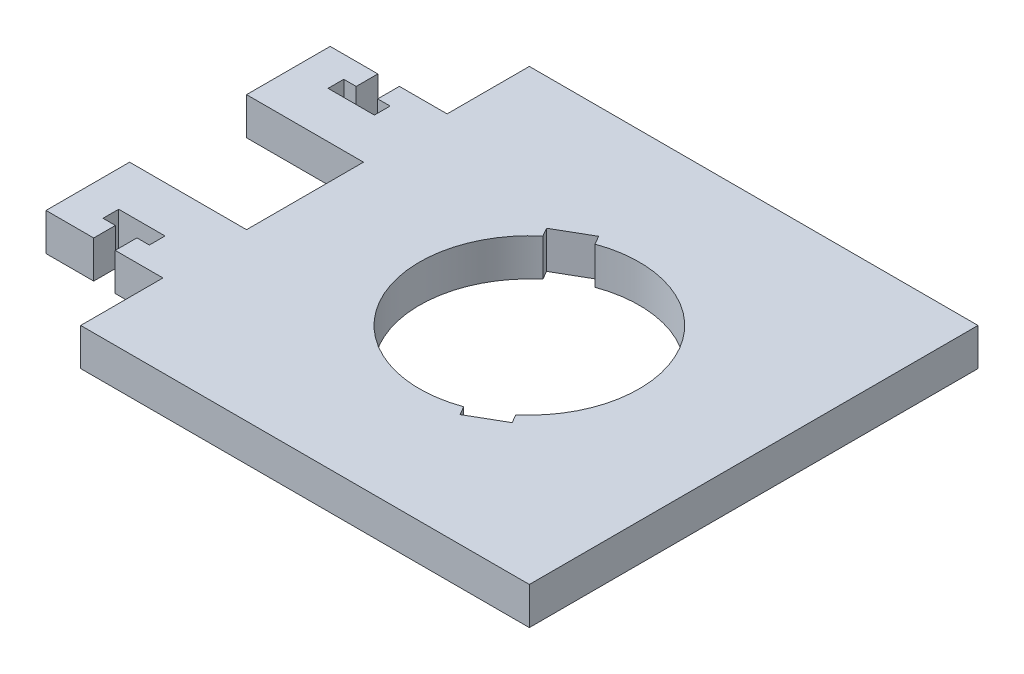
SolidWorks part; units mm, degrees
ref_plane "Front Plane" through (0, 0, 0) normal (0, 0, 1) x (1, 0, 0)
ref_plane "Top Plane" through (0, 0, 0) normal (0, 1, 0) x (1, 0, 0)
ref_plane "Right Plane" through (0, 0, 0) normal (1, 0, 0) x (0, 0, -1)
sketch "Sketch1" plane through (0, 0, 0) normal (0, 1, 0) x (1, 0, 0)
  line L0 (0, 0) -> (38.1, 0) construction
  line L1 (-38.1, -38.1) -> (38.1, -38.1)
  line L2 (-38.1, -38.1) -> (-38.1, -24.13)
  line L3 (-38.1, 38.1) -> (38.1, 38.1)
  line L4 (38.1, -38.1) -> (38.1, 38.1)
  line L5 (-38.1, -38.1) -> (38.1, 38.1) construction
  line L6 (-38.1, 38.1) -> (38.1, -38.1) construction
  line L7 (0, 0) -> (0, -18.5806) construction
  line L8 (9.2265, -15.9809) -> (10.033, -17.3776) construction
  line L11 (7.2271, -18.9976) -> (12.8389, -15.7576)
  line L12 (7.2271, -18.9976) -> (6.3819, -17.5338)
  line L14 (12.8389, -15.7576) -> (11.9937, -14.2938)
  line L15 (0, 0) -> (8.5457, 4.9338) construction
  line L17 (-7.2271, 18.9976) -> (-6.3819, 17.5338)
  line L18 (-12.8389, 15.7576) -> (-7.2271, 18.9976)
  line L19 (-12.8389, 15.7576) -> (-11.9937, 14.2938)
  line L20 (-38.1, -38.1) -> (-38.1, -24.13) construction
  line L21 (-38.1, -24.13) -> (-46.2026, -24.13)
  line L22 (-57.9628, -24.13) -> (-57.9628, -9.9314)
  line L23 (-57.9628, -9.9314) -> (-38.1, -9.9314)
  line L24 (-38.1, 24.13) -> (-46.2026, 24.13)
  line L25 (-57.9628, 24.13) -> (-57.9628, 9.9314)
  line L26 (-57.9628, 9.9314) -> (-38.1, 9.9314)
  line L27 (-38.1, 24.13) -> (-38.1, 38.1)
  line L28 (-38.1, -9.9314) -> (-38.1, 9.9314)
  line L29 (-48.0314, -24.13) -> (-48.0314, -17.78) construction
  line L30 (-51.9684, -17.78) -> (-44.0944, -17.78)
  line L31 (-44.0944, -17.78) -> (-44.0944, -20.447)
  line L32 (-44.0944, -20.447) -> (-46.2026, -20.447)
  line L33 (-46.2026, -20.447) -> (-46.2026, -24.13)
  line L34 (-49.8602, -20.447) -> (-49.8602, -24.13)
  line L35 (-51.9684, -20.447) -> (-49.8602, -20.447)
  line L36 (-51.9684, -17.78) -> (-51.9684, -20.447)
  line L37 (-49.8602, -24.13) -> (-57.9628, -24.13)
  line L38 (-51.9684, 20.447) -> (-49.8602, 20.447)
  line L39 (-49.8602, 20.447) -> (-49.8602, 24.13)
  line L40 (-46.2026, 20.447) -> (-46.2026, 24.13)
  line L41 (-44.0944, 20.447) -> (-46.2026, 20.447)
  line L42 (-44.0944, 17.78) -> (-44.0944, 20.447)
  line L43 (-51.9684, 17.78) -> (-44.0944, 17.78)
  line L44 (-51.9684, 17.78) -> (-51.9684, 20.447)
  line L45 (-49.8602, 24.13) -> (-57.9628, 24.13)
  arc A0 (11.9937, -14.2938) -> (-6.3819, 17.5338) centre (0, 0) ccw
  arc A1 (6.939, -17.0987) -> (11.3384, -14.5587) centre (0, 0) ccw construction
  arc A2 (6.939, -17.0987) -> (11.3384, -14.5587) centre (0, 0) ccw construction
  arc A3 (-11.9937, 14.2938) -> (6.3819, -17.5338) centre (0, 0) ccw
  point P0 (0, 0)
  point P11 (0, -18.5806)
  point P19 (10.033, -17.3776)
  point P25 (0, 0)
  point P35 (0, 0)
  dimension "D2" = 13.97
  dimension "D1" = 45
  dimension "D3" = 76.2
  dimension "D4" = 19.8628
  dimension "D5" = 14.1986
  dimension "D6" = 7.874
  dimension "D7" = 6.35
  dimension "D8" = 2.667
  dimension "D9" = 3.6576
extrude "Boss-Extrude1" add sketch "Sketch1" against normal blind 6.35
